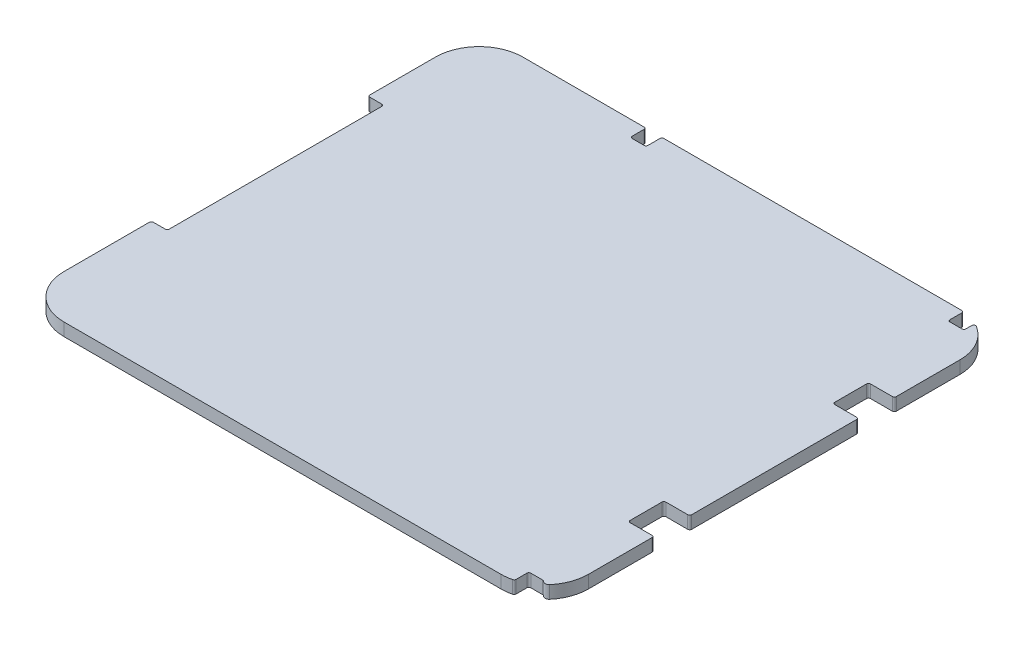
SolidWorks part; units mm, degrees
ref_plane "Plan de face" through (0, 0, 0) normal (0, 0, 1) x (1, 0, 0)
ref_plane "Plan de dessus" through (0, 0, 0) normal (0, 1, 0) x (1, 0, 0)
ref_plane "Plan de droite" through (0, 0, 0) normal (1, 0, 0) x (0, 0, -1)
sketch "Esquisse1" plane through (0, 0, 0) normal (0, 1, 0) x (1, 0, 0)
  line L1 (-33, -28.875) -> (33, -28.875)
  line L2 (-33, -28.875) -> (-33, 28.875)
  line L3 (-33, 28.875) -> (33, 28.875)
  line L4 (33, -28.875) -> (33, 28.875)
  line L5 (-33, -28.875) -> (33, 28.875) construction
  line L6 (-33, 28.875) -> (33, -28.875) construction
  point P0 (0, 0)
  dimension "D1" = 66
  dimension "D2" = 57.75
extrude "Boss.-Extru.1" add sketch "Esquisse1" along normal mid plane 1.6
fillet "Congé1" radius 5.5 4 edges at (33, 0, -28.875) (33, 0, 28.875) (-33, 0, 28.875) (-33, 0, -28.875)
sketch "Esquisse2" plane through (0, 0, 0) normal (0, 1, 0) x (1, 0, 0)
  line L0 (33, -23.375) -> (33, 23.375) construction
  line L1 (-27, -28.375) -> (27, -28.375)
  line L2 (-32.5, -22.875) -> (-32.5, 22.875)
  line L3 (-27, 28.375) -> (27, 28.375)
  line L4 (32.5, -22.875) -> (32.5, 22.875)
  line L5 (-33, 23.375) -> (-33, -23.375) construction
  line L6 (-27.5, -28.875) -> (27.5, -28.875) construction
  line L7 (27.5, 28.875) -> (-27.5, 28.875) construction
  arc A0 (-27, -28.375) -> (-32.5, -22.875) centre (-27, -22.875) cw
  arc A1 (27, -28.375) -> (32.5, -22.875) centre (27, -22.875) ccw
  arc A2 (27, 28.375) -> (32.5, 22.875) centre (27, 22.875) cw
  arc A3 (-32.5, 22.875) -> (-27, 28.375) centre (-27, 22.875) cw
  point P0 (0, 0)
  point P1 (0, 0)
  point P2 (0, 0)
  point P3 (0, 0)
  point P4 (0, 0)
  dimension "D3" = 5.5
  dimension "D1" = 0.5
  dimension "D2" = 0.5
  dimension "D4" = 0.5
  dimension "D5" = 0.5
sketch "Esquisse3" plane through (0, 0, 0) normal (0, 1, 0) x (1, 0, 0)
  line L0 (33, -23.375) -> (33, 23.375) construction
  line L1 (-35, -12.38) -> (-31, -12.38)
  line L2 (-35, -12.38) -> (-35, 14.87)
  line L3 (-35, 14.87) -> (-31, 14.87)
  line L4 (-31, -12.38) -> (-31, 14.87)
  line L5 (-35, -12.38) -> (-31, 14.87) construction
  line L6 (-35, 14.87) -> (-31, -12.38) construction
  line L7 (36.25, -15.125) -> (29.75, -15.125)
  line L8 (-12, 26.875) -> (-10, 26.875)
  line L9 (-12, 26.875) -> (-12, 30.875)
  line L10 (-12, 30.875) -> (-10, 30.875)
  line L11 (-10, 26.875) -> (-10, 30.875)
  line L12 (-12, 26.875) -> (-10, 30.875) construction
  line L13 (-12, 30.875) -> (-10, 26.875) construction
  line L14 (-32.5, -22.875) -> (-32.5, 22.875) construction
  line L15 (36.25, -15.125) -> (36.25, -10.625)
  line L16 (-27, 28.375) -> (27, 28.375) construction
  line L17 (-33, 23.375) -> (-33, -23.375) construction
  line L18 (27.5, 28.875) -> (-27.5, 28.875) construction
  line L19 (-27.5, -28.875) -> (27.5, -28.875) construction
  line L20 (28, 26.875) -> (30, 26.875)
  line L21 (28, 26.875) -> (28, 30.875)
  line L22 (28, 30.875) -> (30, 30.875)
  line L23 (30, 26.875) -> (30, 30.875)
  line L24 (28, 26.875) -> (30, 30.875) construction
  line L25 (28, 30.875) -> (30, 26.875) construction
  line L26 (29, -30.875) -> (31, -30.875)
  line L27 (29, -30.875) -> (29, -26.875)
  line L28 (29, -26.875) -> (31, -26.875)
  line L29 (31, -30.875) -> (31, -26.875)
  line L30 (29, -30.875) -> (31, -26.875) construction
  line L31 (29, -26.875) -> (31, -30.875) construction
  line L32 (36.25, -10.625) -> (29.75, -10.625)
  line L33 (29.75, -15.125) -> (29.75, -10.625)
  line L34 (36.25, -15.125) -> (29.75, -10.625) construction
  line L35 (36.25, -10.625) -> (29.75, -15.125) construction
  line L36 (-27, -28.375) -> (27, -28.375) construction
  line L38 (29.75, 10.625) -> (36.25, 10.625)
  line L39 (29.75, 10.625) -> (29.75, 15.125)
  line L40 (29.75, 15.125) -> (36.25, 15.125)
  line L41 (36.25, 10.625) -> (36.25, 15.125)
  line L42 (29.75, 10.625) -> (36.25, 15.125) construction
  line L43 (29.75, 15.125) -> (36.25, 10.625) construction
  point P0 (-33, 1.245)
  point P5 (30, -28.875)
  point P7 (-11, 28.875)
  point P17 (29, 28.875)
  point P21 (33, -12.875)
  point P39 (33, 12.875)
  point P44 (33, 15.6609)
  dimension "D1" = 27.25
  dimension "D2" = 1.5
  dimension "D3" = 2
  dimension "D4" = 1.5
  dimension "D5" = 21.5
  dimension "D6" = 27.13
  dimension "D7" = 61.5
  dimension "D8" = 62.5
  dimension "D9" = 15.5
  dimension "D10" = 4.5
  dimension "D11" = 3.25
  dimension "D12" = 15.5
extrude "Enlèv. mat.-Extru.1" cut sketch "Esquisse3" against normal through all both and the other way through all
fillet "Congé2" radius 0.25 23 edges at (-12, 0, -28.875) (-10, 0, -28.875) (-12, 0, -26.875) (-10, 0, -26.875) (-33, 0, 12.38) (-31, 0, 12.38) (-31, 0, -14.87) (-33, 0, -14.87) (30, 0, -28.274) (30, 0, -26.875) (28, 0, -26.875) (28, 0, -28.8522) (31, 0, 26.875) (29, 0, 26.875) (29, 0, 28.6665) (33, 0, 10.625) (33, 0, 15.125) (29.75, 0, 15.125) (29.75, 0, 10.625) (33, 0, -10.625) (29.75, 0, -10.625) (33, 0, -15.125) (29.75, 0, -15.125)
fillet "Congé3" radius 0.5 1 edges at (31, 0, 27.6176)
sketch "Esquisse4" plane through (0, 0, 0) normal (0, 1, 0) x (1, 0, 0)
  arc A0 (30, -26.625) -> (30, -20.625) centre (30, -23.625) ccw construction
  arc A1 (30, -20.625) -> (30, -26.625) centre (30, -23.625) ccw construction
  arc A2 (30, -24.975) -> (30, -22.275) centre (30, -23.625) ccw construction
  arc A3 (30, -22.275) -> (30, -24.975) centre (30, -23.625) ccw construction
  arc A4 (30, -26.625) -> (30, -20.625) centre (30, -23.625) ccw
  arc A5 (30, -20.625) -> (30, -26.625) centre (30, -23.625) ccw
  arc A6 (30, -24.975) -> (30, -22.275) centre (30, -23.625) ccw
  arc A7 (30, -22.275) -> (30, -24.975) centre (30, -23.625) ccw
